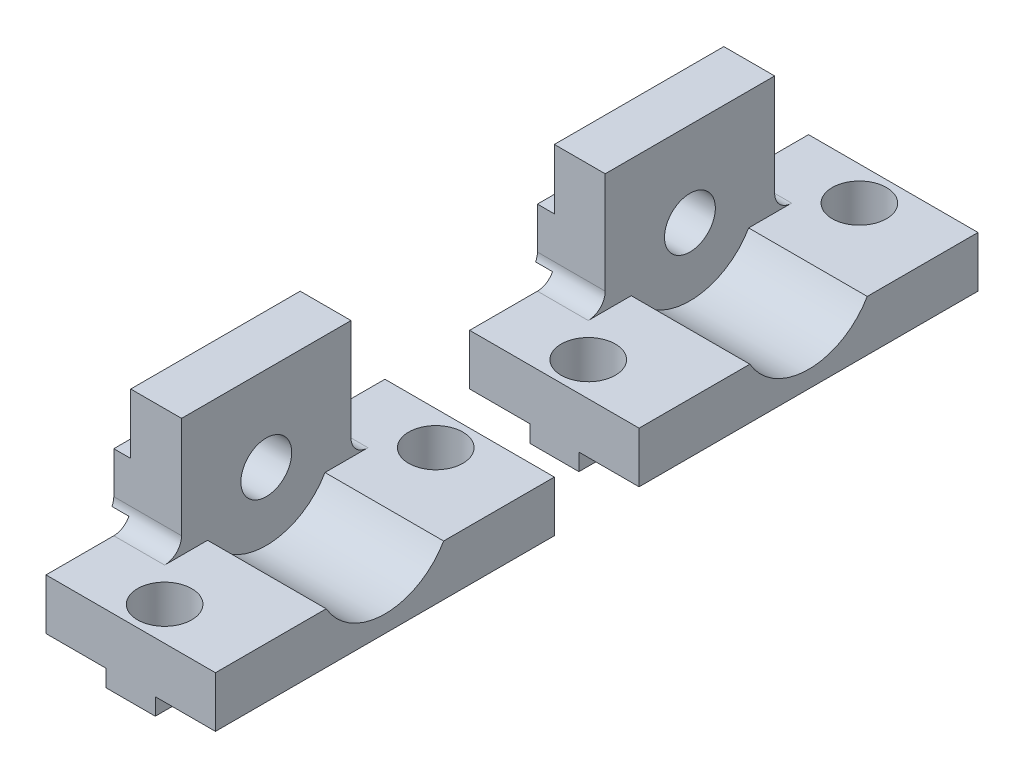
SolidWorks part; units mm, degrees
ref_plane "Front Plane" through (0, 0, 0) normal (0, 0, 1) x (1, 0, 0)
ref_plane "Top Plane" through (0, 0, 0) normal (0, 1, 0) x (1, 0, 0)
ref_plane "Right Plane" through (0, 0, 0) normal (1, 0, 0) x (0, 0, -1)
sketch "Esquisse1" plane through (0, 0, 0) normal (0, 0, 1) x (1, 0, 0)
  line L0 (0, 0) -> (10, 0)
  line L1 (10, 0) -> (10, 3)
  line L2 (10, 3) -> (3, 3)
  line L4 (3, 3) -> (3, 10)
  line L5 (3, 10) -> (0, 10)
  line L6 (0, 10) -> (0, 0)
  point P4 (3, 3)
  point P5 (3.3083, 3)
  dimension "D2" = 10
  dimension "D3" = 3
extrude "Main" add sketch "Esquisse1" along normal blind 20
sketch "Esquisse4" plane through (0, 0, 0) normal (-1, 0, 0) x (0, 0, 1)
  line L0 (20, 10) -> (0, 10) construction
  line L1 (0, 6.45) -> (20, 6.45)
  line L2 (0, 6.45) -> (0, 3.55)
  line L3 (0, 3.55) -> (20, 3.55)
  line L4 (20, 6.45) -> (20, 3.55)
  line L6 (0, 10) -> (0, 0) construction
  line L7 (20, 10) -> (20, 0) construction
  point P6 (10, 2.4141)
  point P8 (0, 7.2269)
  point P9 (10, 10)
  dimension "D1" = 2.9
  dimension "D2" = 3.55
extrude "Vertical Fix" add sketch "Esquisse4" along normal blind 1
sketch "Esquisse2" plane through (0, 0, 0) normal (-1, 0, 0) x (0, 0, 1)
  line L0 (20, 10) -> (0, 10) construction
  line L1 (20, 10) -> (0, 10) construction
  circle A0 centre (10, 5) radius 1.5
  point P9 (10, 10)
  dimension "D1" = 3
  dimension "D2" = 5
extrude "Vertical Hole" cut sketch "Esquisse2" against normal through all both and the other way through all
sketch "Esquisse6" plane through (3, 0, 0) normal (1, 0, 0) x (0, 0, -1)
  line L0 (-20, 3) -> (0, 3) construction
  line L1 (-20, 10) -> (-15, 10)
  line L2 (-20, 10) -> (-20, 3)
  line L3 (-20, 3) -> (-15, 3)
  line L4 (-15, 10) -> (-15, 3)
  line L5 (-20, 10) -> (0, 10) construction
  line L6 (-5, 10) -> (0, 10)
  line L7 (-5, 10) -> (-5, 3)
  line L8 (-5, 3) -> (0, 3)
  line L9 (0, 10) -> (0, 3)
  dimension "D1" = 5
  dimension "D2" = 5
extrude "Cut Borders" cut sketch "Esquisse6" against normal through all
sketch "Esquisse7" plane through (0, 0, 20) normal (0, 0, 1) x (1, 0, 0)
  line L0 (0, 0) -> (10, 0) construction
  line L1 (3.55, 0) -> (6.45, 0)
  line L2 (3.55, 0) -> (3.55, -1)
  line L3 (3.55, -1) -> (6.45, -1)
  line L4 (6.45, 0) -> (6.45, -1)
  line L5 (0, 3) -> (0, 0) construction
  dimension "D1" = 1
  dimension "D2" = 3.55
  dimension "D3" = 2.9
extrude "Boss.-Extru.1" add sketch "Esquisse7" against normal up to surface (20 mm away) up to face at (5, 1.5, 0)
sketch "Esquisse3" plane through (0, 3, 0) normal (0, -1, 0) x (1, 0, 0)
  line L2 (10, 0) -> (0, 0) construction
  line L3 (10, 20) -> (10, 0) construction
  line L4 (10, 20) -> (0, 20) construction
  circle A0 centre (5, 2) radius 1.6
  circle A1 centre (5, 18) radius 1.6
  point P8 (0, 0)
  point P9 (5.4223, 16.9784)
  dimension "D1" = 2
  dimension "D2" = 3.2
  dimension "D3" = 5
  dimension "D4" = 2
extrude "Horizontal Hole" cut sketch "Esquisse3" against normal through all and the other way through all
sketch "Esquisse8" plane through (3, 0, 0) normal (1, 0, 0) x (0, 0, -1)
  circle A0 centre (-10, 5) radius 4
  circle A1 centre (-10, 5) radius 1.5 construction
  dimension "D1" = 8
extrude "Enlèv. mat.-Extru.4" cut sketch "Esquisse8" along normal through all
fillet "Congé1" radius 1 2 edges at (1.5, 3, 15) (1.5, 3, 5)
pattern_linear "Répétition linéaire1" count 2 spacing 25 along (0, 0, -1) of bodies 113
